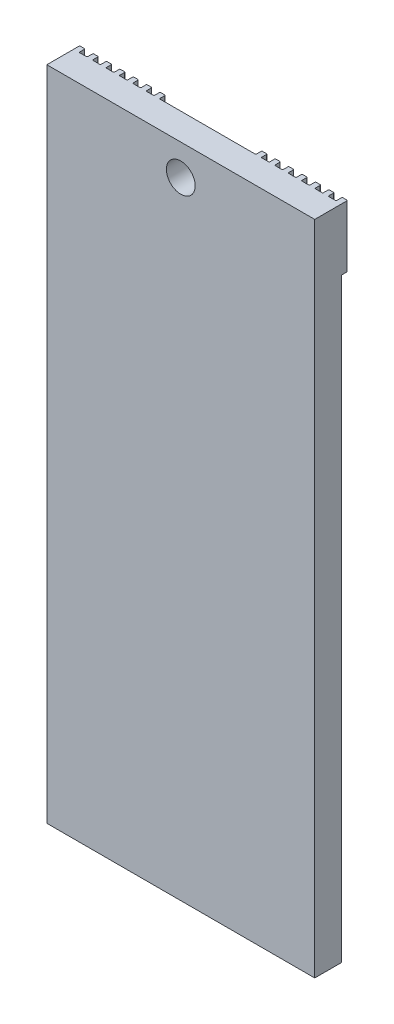
SolidWorks part; units mm, degrees
other "Câmera1"
ref_plane "Plano frontal" through (0, 0, 0) normal (0, 0, 1) x (1, 0, 0)
ref_plane "Plano superior" through (0, 0, 0) normal (0, 1, 0) x (1, 0, 0)
ref_plane "Plano direito" through (0, 0, 0) normal (1, 0, 0) x (0, 0, -1)
sketch "Esboço4" plane through (0, 0, 0) normal (0, 1, 0) x (1, 0, 0)
  line L0 (-19.2, 2.35) -> (-19.2, 1.65)
  line L1 (-20, -2.45) -> (20, -2.45)
  line L2 (-20, -2.45) -> (-20, 2.35)
  line L3 (-19.9, 2.45) -> (-19.3, 2.45)
  line L4 (20, -2.45) -> (20, 2.35)
  line L5 (-19.1, 1.55) -> (-18.1, 1.55)
  line L6 (19.2, 2.35) -> (19.2, 1.65)
  line L7 (19.3, 2.45) -> (19.9, 2.45)
  line L8 (-18, 1.65) -> (-18, 2.35)
  line L9 (-17.9, 2.45) -> (-17.3, 2.45)
  line L10 (-17.2, 2.35) -> (-17.2, 1.65)
  line L11 (-16, 1.65) -> (-16, 2.35)
  line L12 (-15.9, 2.45) -> (-15.3, 2.45)
  line L13 (-15.2, 2.35) -> (-15.2, 1.65)
  line L14 (-14, 1.65) -> (-14, 2.35)
  line L15 (-13.9, 2.45) -> (-13.3, 2.45)
  line L16 (-13.2, 2.35) -> (-13.2, 1.65)
  line L17 (-12, 1.65) -> (-12, 2.35)
  line L18 (-11.9, 2.45) -> (-11.3, 2.45)
  line L19 (-11.2, 2.35) -> (-11.2, 1.65)
  line L20 (-10, 1.65) -> (-10, 2.35)
  line L21 (-9.9, 2.45) -> (-9.3, 2.45)
  line L22 (-9.2, 2.35) -> (-9.2, 1.65)
  line L23 (-8, 1.65) -> (-8, 2.35)
  line L24 (-7.9, 2.45) -> (-7.3, 2.45)
  line L25 (-7.2, 2.35) -> (-7.2, 1.65)
  line L26 (-7.1, 1.55) -> (7.1, 1.55)
  line L27 (-9.1, 1.55) -> (-8.1, 1.55)
  line L28 (-11.1, 1.55) -> (-10.1, 1.55)
  line L29 (-13.1, 1.55) -> (-12.1, 1.55)
  line L30 (-15.1, 1.55) -> (-14.1, 1.55)
  line L31 (-17.1, 1.55) -> (-16.1, 1.55)
  line L32 (17.2, 2.35) -> (17.2, 1.65)
  line L33 (17.3, 2.45) -> (17.9, 2.45)
  line L34 (18, 1.65) -> (18, 2.35)
  line L35 (15.2, 2.35) -> (15.2, 1.65)
  line L36 (15.3, 2.45) -> (15.9, 2.45)
  line L37 (16, 1.65) -> (16, 2.35)
  line L38 (13.2, 2.35) -> (13.2, 1.65)
  line L39 (13.3, 2.45) -> (13.9, 2.45)
  line L40 (14, 1.65) -> (14, 2.35)
  line L41 (11.2, 2.35) -> (11.2, 1.65)
  line L42 (11.3, 2.45) -> (11.9, 2.45)
  line L43 (12, 1.65) -> (12, 2.35)
  line L44 (9.2, 2.35) -> (9.2, 1.65)
  line L45 (9.3, 2.45) -> (9.9, 2.45)
  line L46 (10, 1.65) -> (10, 2.35)
  line L47 (7.2, 2.35) -> (7.2, 1.65)
  line L48 (7.3, 2.45) -> (7.9, 2.45)
  line L49 (8, 1.65) -> (8, 2.35)
  line L50 (8.1, 1.55) -> (9.1, 1.55)
  line L51 (10.1, 1.55) -> (11.1, 1.55)
  line L52 (12.1, 1.55) -> (13.1, 1.55)
  line L53 (14.1, 1.55) -> (15.1, 1.55)
  line L54 (16.1, 1.55) -> (17.1, 1.55)
  line L55 (18.1, 1.55) -> (19.1, 1.55)
  arc A0 (19.9, 2.45) -> (20, 2.35) centre (19.9, 2.35) cw
  arc A1 (19.2, 2.35) -> (19.3, 2.45) centre (19.3, 2.35) cw
  arc A2 (19.1, 1.55) -> (19.2, 1.65) centre (19.1, 1.65) ccw
  arc A3 (18.1, 1.55) -> (18, 1.65) centre (18.1, 1.65) cw
  arc A4 (17.9, 2.45) -> (18, 2.35) centre (17.9, 2.35) cw
  arc A5 (17.2, 2.35) -> (17.3, 2.45) centre (17.3, 2.35) cw
  arc A6 (17.2, 1.65) -> (17.1, 1.55) centre (17.1, 1.65) cw
  arc A7 (16.1, 1.55) -> (16, 1.65) centre (16.1, 1.65) cw
  arc A8 (15.9, 2.45) -> (16, 2.35) centre (15.9, 2.35) cw
  arc A9 (15.2, 2.35) -> (15.3, 2.45) centre (15.3, 2.35) cw
  arc A10 (15.2, 1.65) -> (15.1, 1.55) centre (15.1, 1.65) cw
  arc A11 (14, 1.65) -> (14.1, 1.55) centre (14.1, 1.65) ccw
  arc A12 (13.9, 2.45) -> (14, 2.35) centre (13.9, 2.35) cw
  arc A13 (13.2, 2.35) -> (13.3, 2.45) centre (13.3, 2.35) cw
  arc A14 (13.2, 1.65) -> (13.1, 1.55) centre (13.1, 1.65) cw
  arc A15 (12, 1.65) -> (12.1, 1.55) centre (12.1, 1.65) ccw
  arc A16 (11.9, 2.45) -> (12, 2.35) centre (11.9, 2.35) cw
  arc A17 (11.2, 2.35) -> (11.3, 2.45) centre (11.3, 2.35) cw
  arc A18 (11.2, 1.65) -> (11.1, 1.55) centre (11.1, 1.65) cw
  arc A19 (10, 1.65) -> (10.1, 1.55) centre (10.1, 1.65) ccw
  arc A20 (9.9, 2.45) -> (10, 2.35) centre (9.9, 2.35) cw
  arc A21 (9.2, 2.35) -> (9.3, 2.45) centre (9.3, 2.35) cw
  arc A22 (9.2, 1.65) -> (9.1, 1.55) centre (9.1, 1.65) cw
  arc A23 (8, 1.65) -> (8.1, 1.55) centre (8.1, 1.65) ccw
  arc A24 (7.9, 2.45) -> (8, 2.35) centre (7.9, 2.35) cw
  arc A25 (7.2, 2.35) -> (7.3, 2.45) centre (7.3, 2.35) cw
  arc A26 (7.2, 1.65) -> (7.1, 1.55) centre (7.1, 1.65) cw
  arc A27 (-7.2, 1.65) -> (-7.1, 1.55) centre (-7.1, 1.65) ccw
  arc A28 (-7.3, 2.45) -> (-7.2, 2.35) centre (-7.3, 2.35) cw
  arc A29 (-8, 1.65) -> (-8.1, 1.55) centre (-8.1, 1.65) cw
  arc A30 (-8, 2.35) -> (-7.9, 2.45) centre (-7.9, 2.35) cw
  arc A31 (-9.2, 1.65) -> (-9.1, 1.55) centre (-9.1, 1.65) ccw
  arc A32 (-9.3, 2.45) -> (-9.2, 2.35) centre (-9.3, 2.35) cw
  arc A33 (-10, 2.35) -> (-9.9, 2.45) centre (-9.9, 2.35) cw
  arc A34 (-10, 1.65) -> (-10.1, 1.55) centre (-10.1, 1.65) cw
  arc A35 (-11.2, 1.65) -> (-11.1, 1.55) centre (-11.1, 1.65) ccw
  arc A36 (-11.3, 2.45) -> (-11.2, 2.35) centre (-11.3, 2.35) cw
  arc A37 (-12, 1.65) -> (-12.1, 1.55) centre (-12.1, 1.65) cw
  arc A38 (-12, 2.35) -> (-11.9, 2.45) centre (-11.9, 2.35) cw
  arc A39 (-13.2, 1.65) -> (-13.1, 1.55) centre (-13.1, 1.65) ccw
  arc A40 (-13.3, 2.45) -> (-13.2, 2.35) centre (-13.3, 2.35) cw
  arc A41 (-14, 1.65) -> (-14.1, 1.55) centre (-14.1, 1.65) cw
  arc A42 (-14, 2.35) -> (-13.9, 2.45) centre (-13.9, 2.35) cw
  arc A43 (-15.2, 1.65) -> (-15.1, 1.55) centre (-15.1, 1.65) ccw
  arc A44 (-15.3, 2.45) -> (-15.2, 2.35) centre (-15.3, 2.35) cw
  arc A45 (-16, 1.65) -> (-16.1, 1.55) centre (-16.1, 1.65) cw
  arc A46 (-16, 2.35) -> (-15.9, 2.45) centre (-15.9, 2.35) cw
  arc A47 (-17.2, 1.65) -> (-17.1, 1.55) centre (-17.1, 1.65) ccw
  arc A48 (-17.3, 2.45) -> (-17.2, 2.35) centre (-17.3, 2.35) cw
  arc A49 (-18, 1.65) -> (-18.1, 1.55) centre (-18.1, 1.65) cw
  arc A50 (-18, 2.35) -> (-17.9, 2.45) centre (-17.9, 2.35) cw
  arc A51 (-19.2, 1.65) -> (-19.1, 1.55) centre (-19.1, 1.65) ccw
  arc A52 (-19.2, 2.35) -> (-19.3, 2.45) centre (-19.3, 2.35) ccw
  arc A53 (-20, 2.35) -> (-19.9, 2.45) centre (-19.9, 2.35) cw
  point P0 (0, 0)
  point P62 (19.2, 2.45)
  point P83 (14, 1.55)
  point P92 (12, 1.55)
  point P101 (10, 1.55)
  point P110 (8, 1.55)
  dimension "D2" = 0.1
  dimension "D1" = 7
  dimension "D3" = 14.2
extrude "Ressalto-extrusão2" add sketch "Esboço4" along normal blind 9.2
sketch "Esboço5" plane through (0, 0, -1.55) normal (0, 0, -1) x (-1, 0, 0)
  circle A0 centre (0, 4.6) radius 2.15
  dimension "D1" = 4.3
extrude "Corte-extrusão2" cut sketch "Esboço5" against normal blind 9.2
chamfer "Chanfro2" distance 0.3 angle 45 1 edges at (-2.15, 4.6, -1.55)
sketch "Sketch1" plane through (0, 0, 0) normal (0, -1, 0) x (1, 0, 0)
  line L0 (20, 2.45) -> (20, -2.35) construction
  line L1 (-20, 2.45) -> (20, 2.45)
  line L2 (-20, 2.45) -> (-20, -1.5223)
  line L3 (-20, -1.5223) -> (20, -1.5223)
  line L4 (20, 2.45) -> (20, -1.5223)
extrude "Boss-Extrude1" add sketch "Sketch1" along normal blind 88.9
